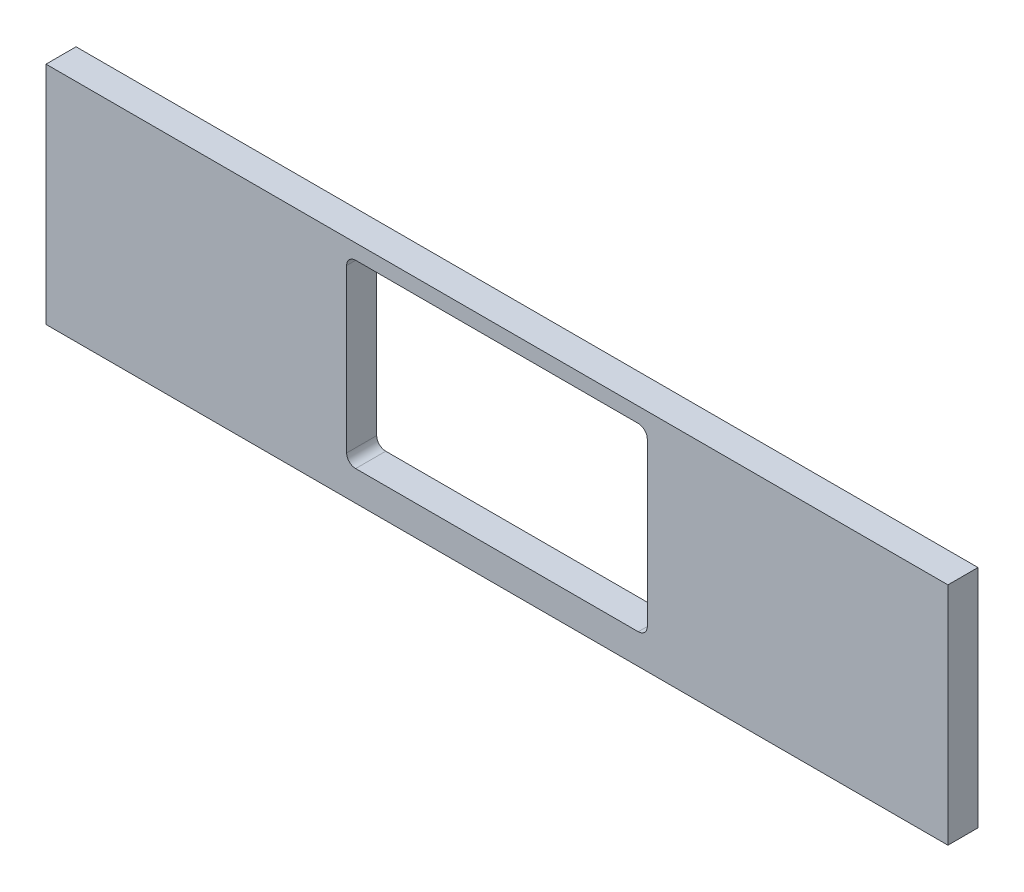
SolidWorks part; units mm, degrees
ref_plane "Ebene vorne" through (0, 0, 0) normal (0, 0, 1) x (1, 0, 0)
ref_plane "Ebene oben" through (0, 0, 0) normal (0, 1, 0) x (1, 0, 0)
ref_plane "Ebene rechts" through (0, 0, 0) normal (1, 0, 0) x (0, 0, -1)
sketch "Skizze1" plane through (0, 0, 0) normal (0, 0, 1) x (1, 0, 0)
  line L0 (-150, -75) -> (-150, 55) construction
  line L1 (150, -150) -> (-150, -150)
  line L2 (150, -150) -> (150, -75)
  line L3 (150, -75) -> (-150, -75)
  line L4 (-150, -150) -> (-150, -75)
  dimension "D1" = 75
extrude "Linear austragen1" add sketch "Skizze1" along normal blind 10
sketch "Skizze2" plane through (0, 0, 10) normal (0, 0, 1) x (1, 0, 0)
  line L0 (-150, -150) -> (150, -150) construction
  line L1 (50, -140) -> (-50, -140)
  line L2 (50, -140) -> (50, -80)
  line L3 (50, -80) -> (-50, -80)
  line L4 (-50, -140) -> (-50, -80)
  line L5 (50, -140) -> (150, -140) construction
  line L7 (-50, -140) -> (-150, -140) construction
  line L8 (-150, 55) -> (-150, -150) construction
  line L9 (150, -150) -> (150, -75) construction
  dimension "D1" = 10
  dimension "D2" = 100
  dimension "D3" = 60
extrude "Schnitt-Linear austragen1" cut sketch "Skizze2" against normal blind 10
fillet "Verrundung1" radius 3 4 edges at (-50, -140, 5) (50, -140, 5) (-50, -80, 5) (50, -80, 5)
